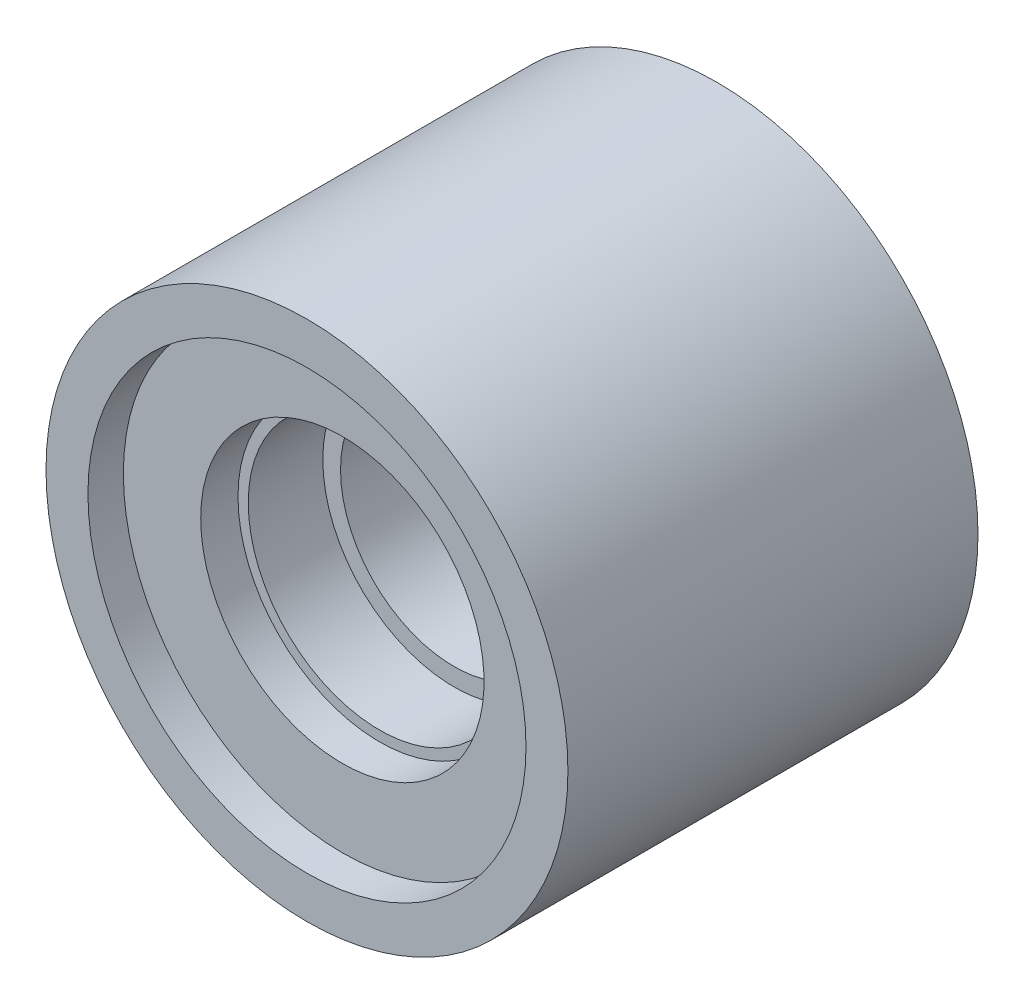
SolidWorks part; units mm, degrees
ref_plane "Спереди" through (0, 0, 0) normal (0, 0, 1) x (1, 0, 0)
ref_plane "Сверху" through (0, 0, 0) normal (0, 1, 0) x (1, 0, 0)
ref_plane "Справа" through (0, 0, 0) normal (1, 0, 0) x (0, 0, -1)
sketch "Эскиз1" plane through (0, 0, 0) normal (0, 0, 1) x (1, 0, 0)
  circle A0 centre (0, 0) radius 14
  dimension "D1" = 28
extrude "Бобышка-Вытянуть1" add sketch "Эскиз1" along normal blind 22
sketch "Эскиз2" plane through (0, 0, 0) normal (0, 0, -1) x (-1, 0, 0)
  circle A0 centre (0, 0) radius 2.95
  dimension "D1" = 5.9
extrude "Вырез-Вытянуть1" cut sketch "Эскиз2" against normal blind 1.1
sketch "Эскиз3" plane through (0, 0, 1.1) normal (0, 0, -1) x (-1, 0, 0)
  circle A0 centre (0, 0) radius 2.6
  dimension "D1" = 5.2
extrude "Вырез-Вытянуть2" cut sketch "Эскиз3" against normal blind 9
sketch "Эскиз5" plane through (0, 0, 22) normal (0, 0, 1) x (1, 0, 0)
  circle A0 centre (0, 0) radius 6.1
  dimension "D1" = 12.2
extrude "Вырез-Вытянуть3" cut sketch "Эскиз5" against normal up to surface (11.9 mm away) up to face at (-2.6, 0, 10.1)
sketch "Эскиз6" plane through (0, 0, 22) normal (0, 0, 1) x (1, 0, 0)
  circle A0 centre (0, 0) radius 7.05
  dimension "D1" = 14.1
extrude "Вырез-Вытянуть4" cut sketch "Эскиз6" against normal offset from surface (7.9 mm away) 4 up to face at (-2.6, 0, 10.1)
sketch "Эскиз7" plane through (0, 0, 22) normal (0, 0, 1) x (1, 0, 0)
  circle A0 centre (0, 0) radius 7.6
  dimension "D1" = 15.2
extrude "Вырез-Вытянуть5" cut sketch "Эскиз7" against normal offset from surface (3.9 mm away) 4 up to face at (-7.05, 0, 14.1)
sketch "Эскиз8" plane through (0, 0, 22) normal (0, 0, 1) x (1, 0, 0)
  circle A0 centre (0, 0) radius 11.75
  dimension "D1" = 23.5
extrude "Вырез-Вытянуть6" cut sketch "Эскиз8" against normal offset from surface (1.9 mm away) 2 up to face at (-7.6, 0, 18.1)
